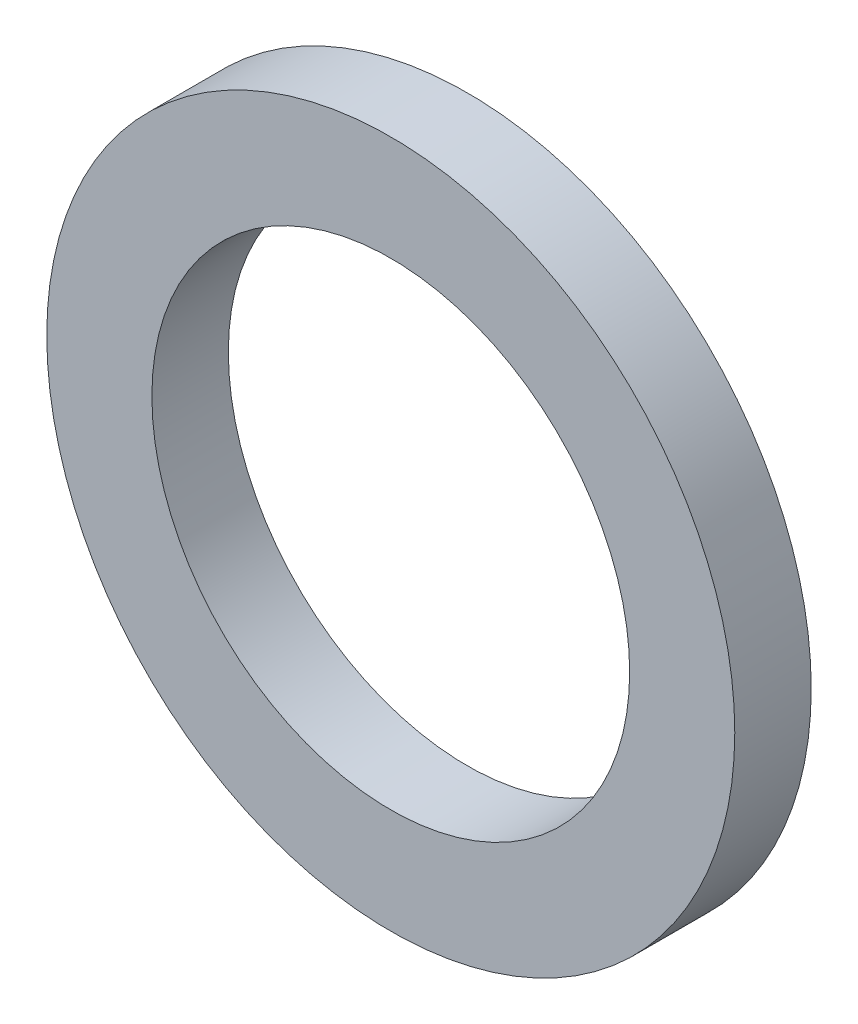
SolidWorks part; units mm, degrees
material "PVC Rigid"
ref_plane "Front Plane" through (0, 0, 0) normal (0, 0, 1) x (1, 0, 0)
ref_plane "Top Plane" through (0, 0, 0) normal (0, 1, 0) x (1, 0, 0)
ref_plane "Right Plane" through (0, 0, 0) normal (1, 0, 0) x (0, 0, -1)
sketch "Sketch1" plane through (0, 0, 0) normal (0, 0, 1) x (1, 0, 0)
  circle A0 centre (0, 0) radius 12.5
  circle A1 centre (0, 0) radius 18
  dimension "D1" = 25
  dimension "D2" = 36
extrude "Boss-Extrude1" add sketch "Sketch1" along normal blind 4
